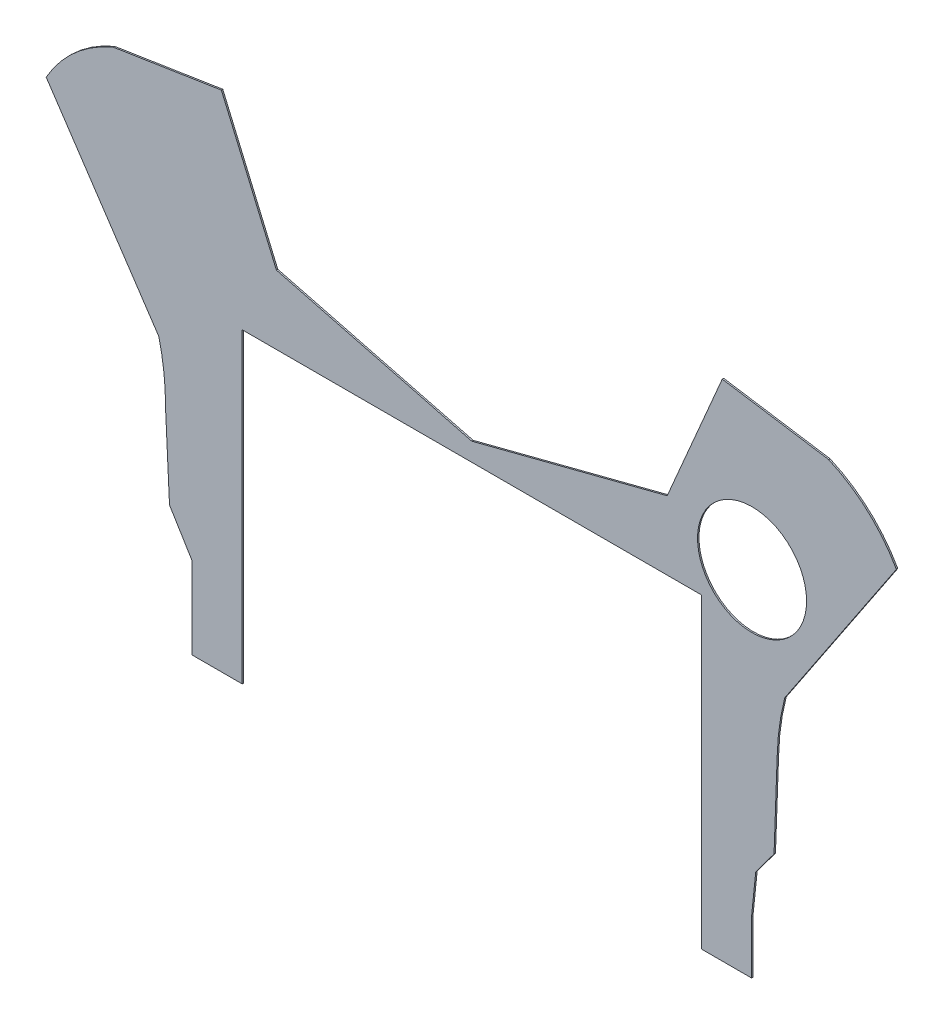
SolidWorks part; units mm, degrees
ref_plane "Alzado" through (0, 0, 0) normal (0, 0, 1) x (1, 0, 0)
ref_plane "Planta" through (0, 0, 0) normal (0, 1, 0) x (1, 0, 0)
ref_plane "Vista lateral" through (0, 0, 0) normal (1, 0, 0) x (0, 0, -1)
sketch "Model" plane through (0, 0, 0) normal (0, 0, 1) x (1, 0, 0)
  line L0 (13.6929, 36.4093) -> (9.7786, 35.7975)
  line L1 (16.8169, 36.8975) -> (20.6506, 27.949)
  line L2 (56.0886, 19.8499) -> (63.8667, 31.4918)
  line L3 (12.4558, 19.8499) -> (4.6086, 31.5703)
  line L4 (53.7709, 1.7757) -> (50.2722, 1.777)
  line L5 (14.7709, 1.777) -> (18.2722, 1.777)
  line L6 (14.7709, 4.477) -> (14.7709, 1.777)
  line L7 (14.7709, 7.477) -> (14.7709, 4.477)
  line L8 (13.2035, 10.0448) -> (14.7709, 7.477)
  line L9 (12.9229, 15.8619) -> (13.2035, 10.0448)
  line L10 (18.2722, 23.1551) -> (33.7722, 23.1551)
  line L11 (18.2722, 1.777) -> (18.2722, 23.1551)
  line L12 (50.2722, 23.1551) -> (50.2722, 1.777)
  line L13 (34.7722, 23.1551) -> (50.2722, 23.1551)
  line L14 (20.6506, 27.949) -> (34.2722, 24.4317)
  line L15 (34.2722, 24.4317) -> (47.8937, 27.949)
  line L16 (47.8937, 27.949) -> (51.7313, 36.9064)
  line L17 (55.3409, 10.0448) -> (55.5594, 16.0693)
  line L18 (54.0656, 8.3317) -> (55.3409, 10.0448)
  line L19 (53.7709, 5.477) -> (54.0656, 8.3317)
  line L20 (53.7709, 1.7757) -> (53.7709, 5.477)
  line L21 (16.8169, 36.8975) -> (13.6929, 36.4093)
  line L22 (9.7786, 35.7975) -> (9.2912, 35.7213)
  line L23 (59.142, 35.7599) -> (51.7313, 36.9064)
  line L24 (33.7722, 23.1551) -> (34.7722, 23.1551)
  arc A0 (56.0886, 19.8499) -> (55.5594, 16.0693) centre (72.2138, 15.6656) ccw
  circle A1 centre (53.8089, 26.4413) radius 3.8007
  arc A2 (9.2912, 35.7213) -> (4.6086, 31.5703) centre (12.9592, 26.8669) ccw
  arc A3 (12.9229, 15.8619) -> (12.4558, 19.8499) centre (-3.3381, 15.9785) ccw
  arc A4 (63.8667, 31.4918) -> (59.142, 35.7599) centre (55.1498, 26.5913) ccw
extrude "Saliente-Extruir1" add sketch "Model" along normal blind 0.1
